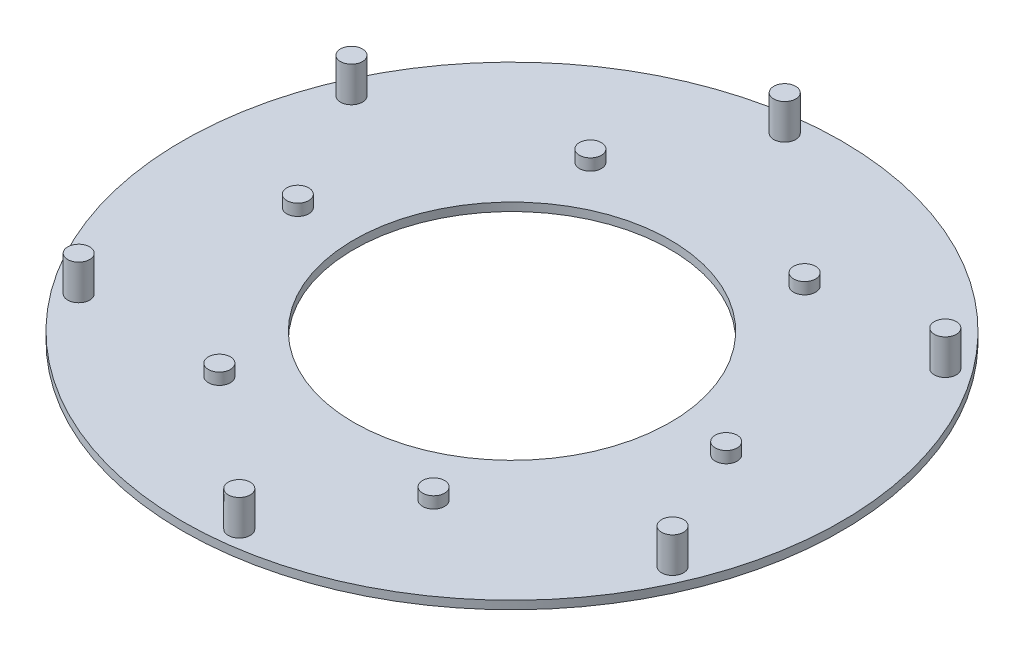
SolidWorks part; units mm, degrees
ref_plane "Front Plane" through (0, 0, 0) normal (0, 0, 1) x (1, 0, 0)
ref_plane "Top Plane" through (0, 0, 0) normal (0, 1, 0) x (1, 0, 0)
ref_plane "Right Plane" through (0, 0, 0) normal (1, 0, 0) x (0, 0, -1)
sketch "Sketch1" plane through (0, 0, 0) normal (0, 1, 0) x (1, 0, 0)
  circle A0 centre (0, 0) radius 200
  circle A1 centre (0, 0) radius 96
  dimension "D1" = 400
  dimension "D2" = 192
extrude "Boss-Extrude1" add sketch "Sketch1" along normal blind 5
sketch "Sketch2" plane through (0, 5, 0) normal (0, 1, 0) x (1, 0, 0)
  line L0 (0, 0) -> (130, 0) construction
  line L2 (151.1251, 111.8267) -> (0, 0) construction
  circle A0 centre (151.1251, 111.8267) radius 3.5
  circle A1 centre (130, 0) radius 2
  dimension "D1" = 4
  dimension "D2" = 7
  dimension "D3" = 130
  dimension "D4" = 188
  dimension "D5" = 36.5
extrude "Cut-Extrude1" cut sketch "Sketch2" against normal up to next (5 mm away)
pattern_circular "CirPattern1" count 6 over 360 about axis through (0, 0, 0) along (0, 1, 0) of "Cut-Extrude1"
scale "Scale2" scale about centroid uniform scaling yes scale factor 0.225
sketch "Sketch3" plane through (0, 1.9375, 0) normal (0, -1, 0) x (1, 0, 0)
  circle A12 centre (-38.7916, -16.8671) radius 1.5
  dimension "D1" = 3
extrude "Boss-Extrude2" add sketch "Sketch3" against normal blind 5.93
sketch "Sketch4" plane through (0, 1.9375, 0) normal (0, -1, 0) x (1, 0, 0)
  circle A12 centre (-14.625, 25.3312) radius 1.5
  circle A13 centre (14.625, 25.3312) radius 1.5
  circle A14 centre (29.25, 0) radius 1.5
  circle A15 centre (14.625, -25.3312) radius 1.5
  circle A16 centre (-14.625, -25.3312) radius 1.5
  circle A17 centre (-29.25, 0) radius 1.5
  dimension "D1" = 3
  dimension "D2" = 6
extrude "Boss-Extrude3" add sketch "Sketch4" against normal blind 2.7
pattern_circular "CirPattern2" count 6 over 360 about axis through (0, 0, 0) along (0, 1, 0) of "Boss-Extrude2"
